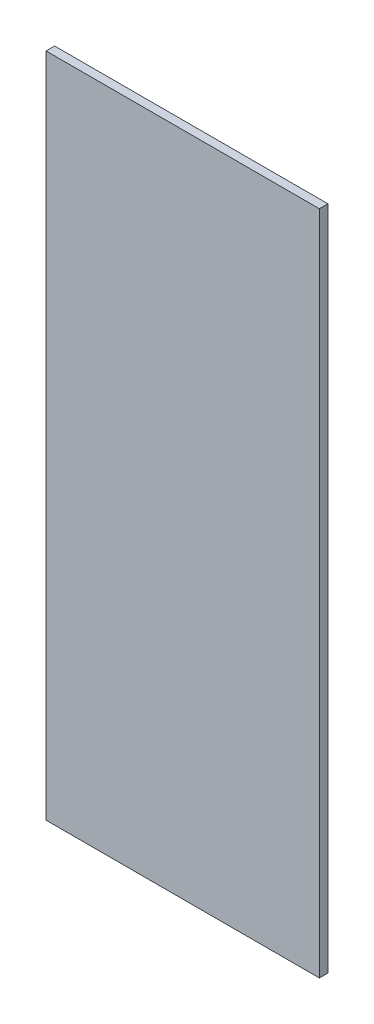
SolidWorks part; units mm, degrees
ref_plane "Alzado" through (0, 0, 0) normal (0, 0, 1) x (1, 0, 0)
ref_plane "Planta" through (0, 0, 0) normal (0, 1, 0) x (1, 0, 0)
ref_plane "Vista lateral" through (0, 0, 0) normal (1, 0, 0) x (0, 0, -1)
sketch "Croquis2" plane through (0, 0, 0) normal (0, 1, 0) x (1, 0, 0)
  line L5 (-101.6, 3.175) -> (101.6, 3.175)
  line L6 (-101.6, 3.175) -> (-101.6, -3.175)
  line L7 (-101.6, -3.175) -> (101.6, -3.175)
  line L8 (101.6, 3.175) -> (101.6, -3.175)
  line L9 (-101.6, 3.175) -> (101.6, -3.175) construction
  line L10 (-101.6, -3.175) -> (101.6, 3.175) construction
  point P0 (0, 0)
  dimension "D1" = 203.2
  dimension "D2" = 6.35
extrude "Saliente-Extruir1" add sketch "Croquis2" along normal blind 495.3
sketch "Croquis4" plane through (0, 0, 3.175) normal (0, 0, 1) x (1, 0, 0)
  line L0 (0, 495.3) -> (-53.975, 495.3) construction
  line L1 (-101.6, 495.3) -> (101.6, 495.3) construction
  line L2 (0, 495.3) -> (53.975, 495.3) construction
  dimension "D1" = 53.975
  dimension "D2" = 53.975
ref_plane "Izquierdo" through (-53.975, 0, 0) normal (-1, 0, 0) x (0, 0, 1)
ref_plane "Derecho" through (53.975, 0, 0) normal (1, 0, 0) x (0, 0, -1)
ref_plane "Medio" through (0, 254, 0) normal (0, 1, 0) x (1, 0, 0)
